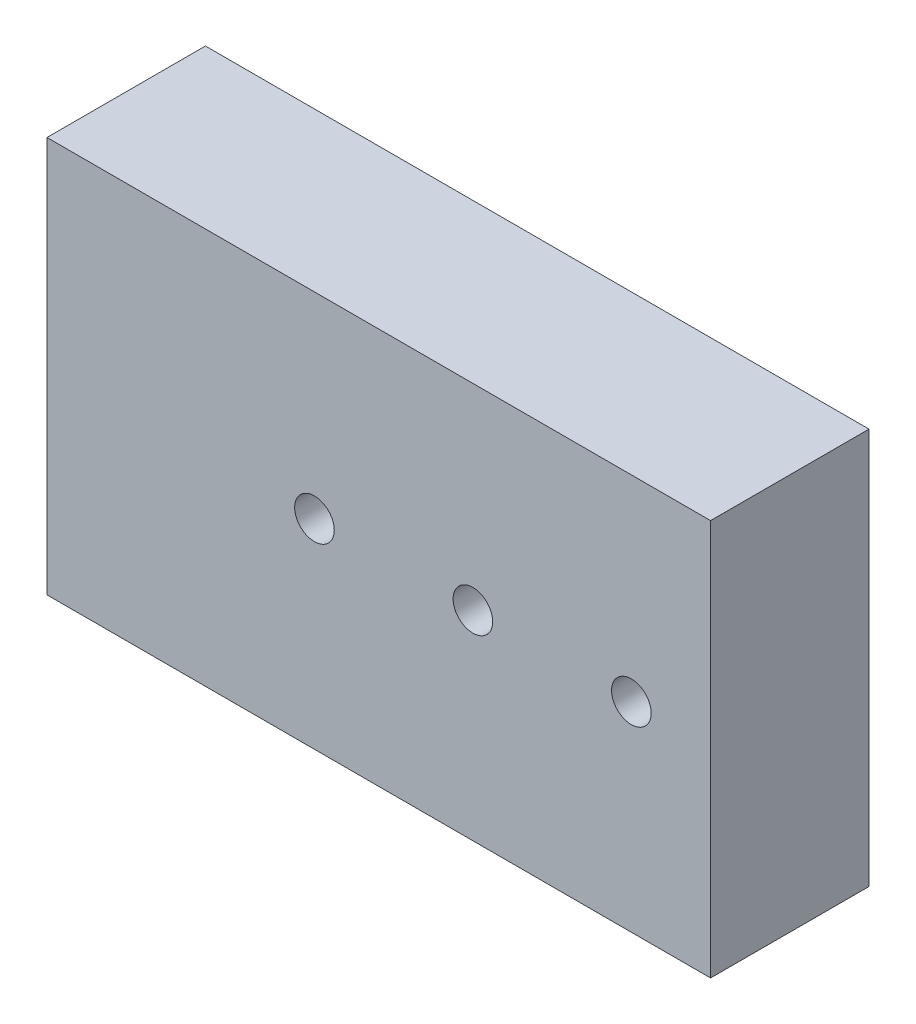
SolidWorks part; units mm, degrees
material "Delrin 2700 NC010, Low Viscosity Acetal Copolymer (SS)"
ref_plane "Front Plane" through (0, 0, 0) normal (0, 0, 1) x (1, 0, 0)
ref_plane "Top Plane" through (0, 0, 0) normal (0, 1, 0) x (1, 0, 0)
ref_plane "Right Plane" through (0, 0, 0) normal (1, 0, 0) x (0, 0, -1)
sketch "Sketch1" plane through (0, 0, 0) normal (1, 0, 0) x (0, 0, -1)
  line L0 (25.4, 0) -> (25.4, 108.2)
  line L1 (0, 0) -> (25.4, 0)
  line L2 (0, 0) -> (0, 63.5)
  line L3 (0, 63.5) -> (25.4, 63.5)
  line L4 (25.4, 0) -> (25.4, 63.5)
  line L5 (25.4, 108.2) -> (0, 108.2)
  line L6 (0, 108.2) -> (0, 0)
  line L8 (228.6, 108.2) -> (25.4, 108.2) construction
  dimension "D1" = 25.4
  dimension "D2" = 63.5
  dimension "D3" = 44.7
extrude "Boss-Extrude1" add sketch "Sketch1" along normal up to surface (106.376 mm away) contours L3 L2 L1 L0
hole_wizard "1/4 (0.25) Diameter Hole1" positions "Sketch2" profile "Sketch3" hole size "1/4" standard "ANSI Inch" end condition through all
sketch "Sketch2" plane through (0, 0, 0) normal (0, 0, 1) x (1, 0, 0)
  point P8 (42.876, 32)
  point P11 (93.676, 32)
  point P14 (68.276, 32)
sketch "Sketch3" plane through (42.876, 32, 0) normal (1, 0, 0) x (0, -1, 0)
  line L0 (0, 0) -> (0, 25.4)
  line L1 (0, 25.4) -> (3.175, 25.4)
  line L2 (3.175, 25.4) -> (3.175, 0)
  line L5 (3.175, 0) -> (0, 0)
  line L11 (0, -6.35) -> (0, 107.95) construction
  dimension "Thru Hole Dia." = 6.35
  dimension "Thru Hole Depth" = 25.4
hole_wizard "Ø6.0mm Dowel Hole1" positions "Sketch4" profile "Sketch6" hole size "Ø6.0" standard "ANSI Metric"
sketch "Sketch4" plane through (0, 0, 0) normal (-1, 0, 0) x (0, 0, 1)
  point P6 (-15.4, 7)
  point P9 (-15.4, 53)
sketch "Sketch6" plane through (0, 7, -15.4) normal (0, 1, 0) x (0, 0, 1)
  line L0 (0, 0) -> (0, 10.8927)
  line L1 (0, 10.8927) -> (3.15, 9)
  line L2 (3.15, 9) -> (3.15, 0)
  line L5 (3.15, 0) -> (0, 0)
  line L10 (0, 10.8927) -> (-3.15, 9) construction
  line L11 (0, -6.35) -> (0, 107.95) construction
  dimension "Hole Dia." = 6.3
  dimension "Hole Depth" = 9
  dimension "Drill Angle" = 118
